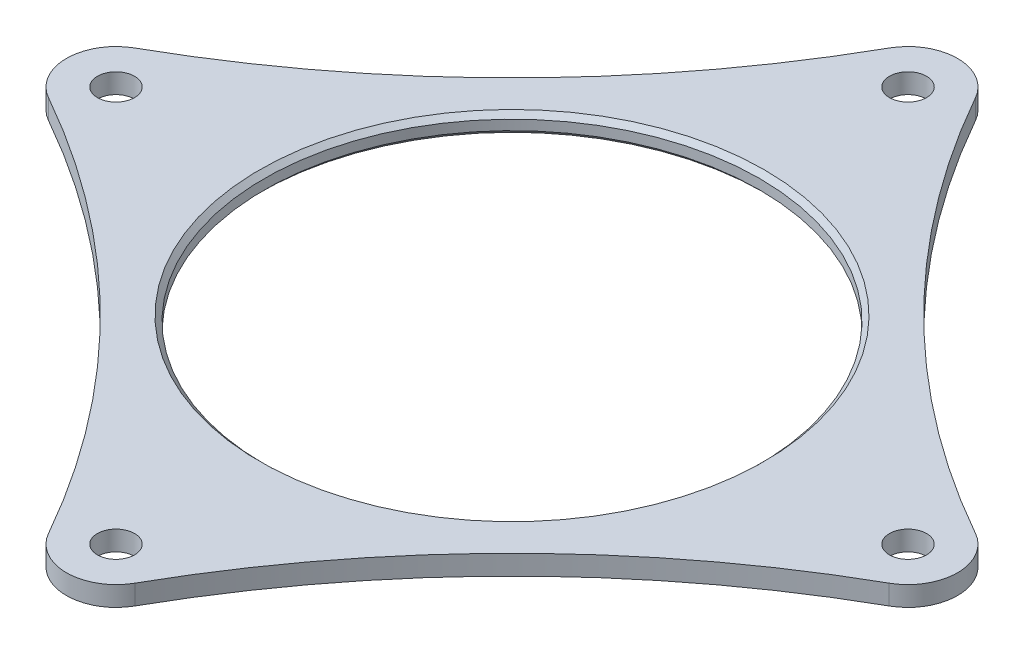
SolidWorks part; units mm, degrees
ref_plane "Front Plane" through (0, 0, 0) normal (0, 0, 1) x (1, 0, 0)
ref_plane "Top Plane" through (0, 0, 0) normal (0, 1, 0) x (1, 0, 0)
ref_plane "Right Plane" through (0, 0, 0) normal (1, 0, 0) x (0, 0, -1)
sketch "Sketch1" plane through (0, 0, 0) normal (0, 1, 0) x (1, 0, 0)
  line L1 (-114.3, -114.3) -> (114.3, -114.3)
  line L2 (-114.3, -114.3) -> (-114.3, 114.3)
  line L3 (-114.3, 114.3) -> (114.3, 114.3)
  line L4 (114.3, -114.3) -> (114.3, 114.3)
  line L5 (-114.3, -114.3) -> (114.3, 114.3) construction
  line L6 (-114.3, 114.3) -> (114.3, -114.3) construction
  point P0 (0, 0)
  dimension "D1" = 228.6
extrude "Boss-Extrude1" add sketch "Sketch1" along normal blind 5.08
sketch "Sketch2" plane through (0, 5.08, 0) normal (0, 1, 0) x (1, 0, 0)
  circle A0 centre (0, 0) radius 63.5
  circle A1 centre (0, 0) radius 101.6 construction
  dimension "D2" = 127
  dimension "D3" = 203.2
extrude "Cut-Extrude1" cut sketch "Sketch2" against normal through all
sketch "Sketch3" plane through (0, 5.08, 0) normal (0, 1, 0) x (1, 0, 0)
  line L0 (0, 101.6) -> (0, 0) construction
  line L1 (0, 0) -> (101.6, 0) construction
  line L4 (114.3, 114.3) -> (-114.3, 114.3) construction
  line L5 (114.3, -114.3) -> (114.3, 114.3) construction
  line L6 (114.3, 114.3) -> (0, 114.3)
  line L7 (114.3, 0) -> (114.3, 114.3)
  circle A0 centre (101.6, 0) radius 4.7625 construction
  circle A1 centre (0, 101.6) radius 4.7625 construction
  arc A2 (11.0674, 107.8293) -> (0, 114.3) centre (0, 101.6) ccw
  arc A3 (114.3, 0) -> (107.8293, 11.0674) centre (101.6, 0) ccw
  arc A4 (11.0674, 107.8293) -> (107.8293, 11.0674) centre (232.4144, 232.4144) ccw
  dimension "D2" = 9.525
  dimension "D3" = 25.4
  dimension "D4" = 254
  dimension "D1" = 101.6
extrude "Cut-Extrude2" cut sketch "Sketch3" against normal through all
pattern_circular "CirPattern1" count 4 over 360 about axis through (0, 0, 0) along (0, 1, 0) of "Cut-Extrude2"
hole_wizard "3/8 (0.375) Diameter Hole1" positions "Sketch6" profile "Sketch7" hole size "3/8" standard "ANSI Inch" end condition up to next
sketch "Sketch6" plane through (0, 5.08, 0) normal (0, 1, 0) x (1, 0, 0)
  arc A3 (107.8293, -11.0674) -> (107.8293, 11.0674) centre (101.6, 0) ccw construction
  arc A4 (107.8293, -11.0674) -> (107.8293, 11.0674) centre (101.6, 0) ccw
  point P0 (101.6, 0)
  point P11 (101.6, 0)
sketch "Sketch7" plane through (101.6, 5.08, 0) normal (1, 0, 0) x (0, 0, 1)
  line L0 (0, 0) -> (0, 5.081)
  line L1 (0, 5.081) -> (4.7625, 5.081)
  line L2 (4.7625, 5.081) -> (4.7625, 0)
  line L5 (4.7625, 0) -> (0, 0)
  line L11 (0, -6.35) -> (0, 107.95) construction
  dimension "Thru Hole Dia." = 9.525
  dimension "Thru Hole Depth" = 5.081
pattern_circular "CirPattern2" count 4 over 360 about axis through (0, 0, 0) along (0, 1, 0) of "3/8 (0.375) Diameter Hole1"
chamfer "Chamfer1" distance 1.27 angle 45 2 edges at (0, 5.08, 63.5) (0, 0, 63.5)
